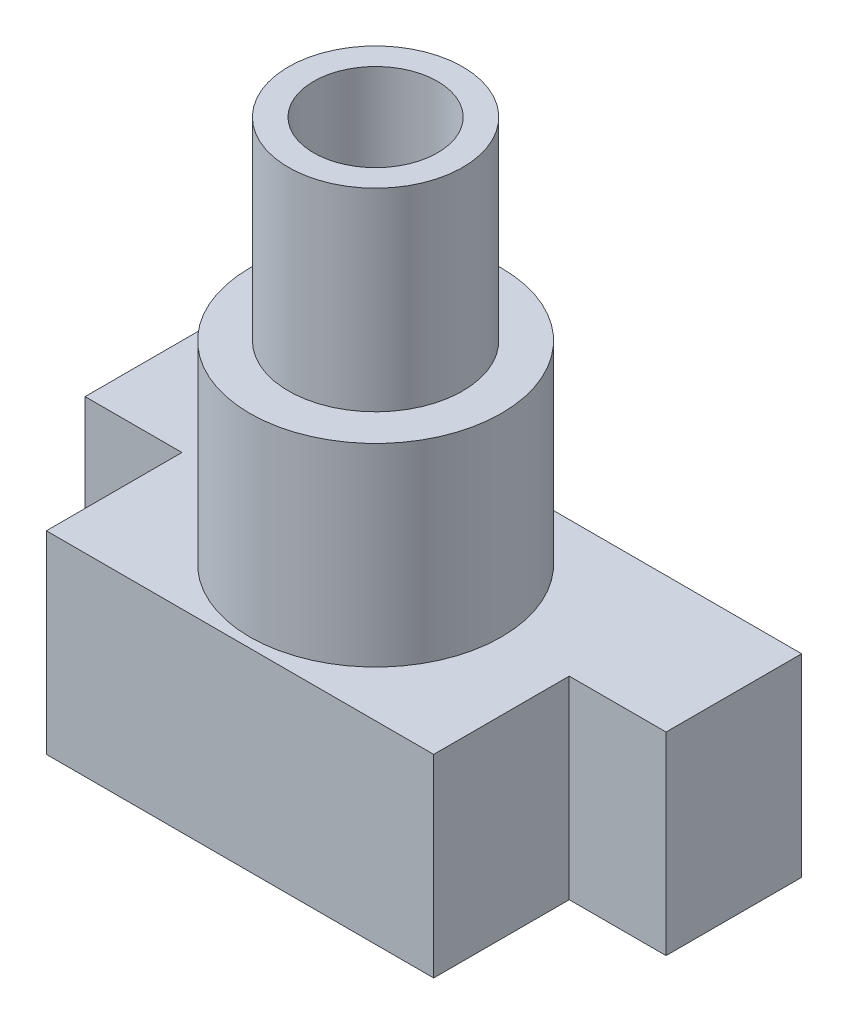
SolidWorks part; units mm, degrees
ref_plane "Front Plane" through (0, 0, 0) normal (0, 0, 1) x (1, 0, 0)
ref_plane "Top Plane" through (0, 0, 0) normal (0, 1, 0) x (1, 0, 0)
ref_plane "Right Plane" through (0, 0, 0) normal (1, 0, 0) x (0, 0, -1)
sketch "Sketch2" plane through (0, 0, 0) normal (0, 1, 0) x (1, 0, 0)
  line L0 (-5, 0) -> (-7.5, 0)
  line L1 (-5, -3.5) -> (5, -3.5)
  line L2 (-5, -3.5) -> (-5, 0)
  line L3 (-5, 3.5) -> (5, 3.5)
  line L4 (5, -3.5) -> (5, 0)
  line L5 (-5, -3.5) -> (5, 3.5) construction
  line L6 (-5, 3.5) -> (5, -3.5) construction
  line L7 (3.1754, 0) -> (1.5877, 2.75) construction
  line L8 (1.5877, 2.75) -> (-1.5877, 2.75) construction
  line L9 (-1.5877, 2.75) -> (-3.1754, 0) construction
  line L10 (-3.1754, 0) -> (-1.5877, -2.75) construction
  line L11 (-1.5877, -2.75) -> (1.5877, -2.75) construction
  line L12 (1.5877, -2.75) -> (3.1754, 0) construction
  line L13 (-7.5, 0) -> (-7.5, 3.5)
  line L14 (-7.5, 3.5) -> (-5, 3.5)
  line L15 (5, 3.5) -> (7.5, 3.5)
  line L16 (7.5, 3.5) -> (7.5, 0)
  line L17 (7.5, 0) -> (5, 0)
  line L18 (5, 3.5) -> (5, 0) construction
  line L19 (-5, 3.5) -> (-5, 0) construction
  circle A0 centre (0, 0) radius 2.75 construction
  point P0 (0, 0)
  dimension "D1" = 5.5
  dimension "D2" = 7
  dimension "D3" = 10
  dimension "D5" = 15
extrude "Boss-Extrude1" add sketch "Sketch2" along normal blind 5
sketch "Sketch3" plane through (0, 0, 0) normal (0, -1, 0) x (1, 0, 0)
  line L1 (3.1754, 0) -> (1.5877, 2.75)
  line L2 (1.5877, 2.75) -> (-1.5877, 2.75)
  line L3 (-1.5877, 2.75) -> (-3.1754, 0)
  line L4 (-3.1754, 0) -> (-1.5877, -2.75)
  line L5 (-1.5877, -2.75) -> (1.5877, -2.75)
  line L6 (1.5877, -2.75) -> (3.1754, 0)
  circle A0 centre (0, 0) radius 2.75 construction
  dimension "D1" = 5.5
extrude "Cut-Extrude1" cut sketch "Sketch3" against normal blind 2.5
sketch "Sketch4" plane through (0, 0, 0) normal (0, 0, 1) x (1, 0, 0)
  line L0 (0, 0) -> (0, 20.4847) construction
  line L1 (1.6, 5) -> (1.6, 15)
  line L2 (-5, 5) -> (5, 5) construction
  line L3 (1.6, 15) -> (2.25, 15)
  line L4 (2.25, 15) -> (2.25, 10)
  line L5 (2.25, 10) -> (3.25, 10)
  line L6 (3.25, 10) -> (3.25, 5)
  line L7 (3.25, 5) -> (1.6, 5)
  dimension "D1" = 3.2
  dimension "D2" = 4.5
  dimension "D3" = 5
  dimension "D4" = 6.5
  dimension "D5" = 5
revolve "Revolve1" add sketch "Sketch4" angle 360 about L0
sketch "Sketch5" plane through (0, 2.5, 0) normal (0, -1, 0) x (1, 0, 0)
  circle A0 centre (0, 0) radius 1.6
  circle A1 centre (0, 0) radius 1.6 construction
extrude "Cut-Extrude2" cut sketch "Sketch5" against normal through all
